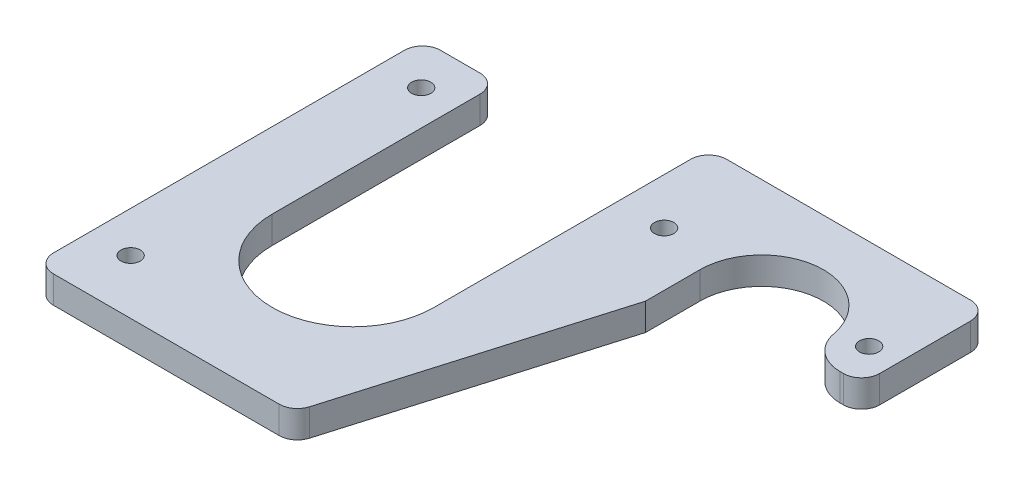
SolidWorks part; units mm, degrees
material "PC High Viscosity"
ref_plane "Front Plane" through (0, 0, 0) normal (0, 0, 1) x (1, 0, 0)
ref_plane "Top Plane" through (0, 0, 0) normal (0, 1, 0) x (1, 0, 0)
ref_plane "Right Plane" through (0, 0, 0) normal (1, 0, 0) x (0, 0, -1)
sketch "Sketch1" plane through (0, 0, 0) normal (0, 1, 0) x (1, 0, 0)
  line L0 (28.575, 81.7563) -> (28.575, 160.782)
  line L1 (0, 0) -> (180.975, 0) construction
  line L2 (0, 0) -> (0, 160.782) construction
  line L3 (28.575, 177.8) -> (180.975, 177.8) construction
  line L4 (180.975, 0) -> (180.975, 177.8) construction
  line L6 (0, 160.782) -> (0, 0)
  line L7 (0, 0) -> (82.55, 0)
  line L9 (80.9625, 81.7563) -> (80.9625, 177.8)
  line L10 (80.9625, 177.8) -> (121.7041, 177.8)
  line L13 (180.975, 139.7) -> (180.975, 177.8)
  line L14 (180.975, 177.8) -> (121.7041, 177.8)
  line L16 (118.11, 139.7) -> (118.11, 120.65)
  line L17 (82.55, 0) -> (118.11, 120.65)
  line L18 (161.29, 139.7) -> (161.29, 120.65)
  line L19 (180.975, 139.7) -> (180.975, 120.65)
  line L20 (180.975, 120.65) -> (161.29, 120.65)
  line L21 (0, 160.782) -> (28.575, 160.782)
  arc A0 (161.29, 139.7) -> (118.11, 139.7) centre (139.7, 139.7) ccw
  arc A1 (28.575, 81.7563) -> (80.9625, 81.7563) centre (54.7687, 81.7563) ccw
  dimension "D3" = 43.18
  dimension "D5" = 52.3875
  dimension "D1" = 177.8
  dimension "D2" = 180.975
  dimension "D4" = 38.1
  dimension "D6" = 81.7563
  dimension "D7" = 54.7687
  dimension "D8" = 139.7
  dimension "D9" = 19.05
  dimension "D10" = 82.55
  dimension "D11" = 121.7041
  dimension "D12" = 160.782
extrude "Boss-Extrude1" add sketch "Sketch1" along normal blind 9.525
sketch "Sketch2" plane through (0, 9.525, 0) normal (0, 1, 0) x (1, 0, 0)
  line L1 (0, 0) -> (94.3317, 0)
  line L2 (0, 0) -> (0, 25.4)
  line L3 (0, 25.4) -> (94.3317, 25.4)
  line L4 (94.3317, 0) -> (94.3317, 25.4)
  dimension "D1" = 25.4
extrude "Cut-Extrude1" cut sketch "Sketch2" against normal through all
fillet "Fillet1" radius 6.35 1 edges at (0, 4.7625, -25.4)
fillet "Fillet2" radius 6.35 4 edges at (0, 4.7625, -160.782) (180.975, 4.7625, -177.8) (180.975, 4.7625, -120.65) (90.0363, 4.7625, -25.4)
hole_wizard "1/4 Clearance Hole1" positions "Sketch3" profile "Sketch4" hole size "1/4" standard "ANSI Inch" end condition through all
sketch "Sketch3" plane through (0, 9.525, 0) normal (0, 1, 0) x (1, 0, 0)
  line L1 (28.575, 160.782) -> (6.35, 160.782) construction
  line L4 (161.29, 120.65) -> (174.625, 120.65) construction
  line L10 (99.2378, 131.2063) -> (99.2378, 177.8) construction
  line L11 (174.625, 177.8) -> (80.9625, 177.8) construction
  line L13 (17.4625, 95.25) -> (5.6328, 95.25) construction
  line L15 (0, 154.432) -> (0, 31.75) construction
  line L20 (170.9229, 130.175) -> (170.9229, 177.8) construction
  line L21 (174.625, 177.8) -> (80.9625, 177.8) construction
  line L24 (28.575, 118.8041) -> (0, 118.8041) construction
  line L25 (28.575, 81.7563) -> (28.575, 160.782) construction
  line L27 (14.2875, 118.8041) -> (14.2875, 63.4643) construction
  line L29 (118.11, 120.65) -> (118.11, 139.7) construction
  line L30 (180.975, 127) -> (180.975, 171.45) construction
  point P0 (14.2875, 146.05)
  point P2 (14.2875, 44.45)
  point P4 (99.2378, 146.05)
  point P6 (170.9229, 146.05)
  dimension "D1" = 25.4
  dimension "D2" = 14.732
  dimension "D3" = 18.8722
  dimension "D4" = 10.052
  dimension "D5" = 101.6
sketch "Sketch4" plane through (14.2875, 9.525, -146.05) normal (1, 0, 0) x (0, 0, 1)
  line L0 (0, 0) -> (0, 9.525)
  line L1 (0, 9.525) -> (3.3782, 9.525)
  line L2 (3.3782, 9.525) -> (3.3782, 0)
  line L5 (3.3782, 0) -> (0, 0)
  line L11 (0, -6.35) -> (0, 107.95) construction
  dimension "Thru Hole Dia." = 6.7564
  dimension "Thru Hole Depth" = 9.525
sketch "Sketch5" plane through (0, 9.525, 0) normal (0, 1, 0) x (1, 0, 0)
  line L0 (161.29, 133.35) -> (180.975, 133.35)
  line L1 (161.29, 139.7) -> (161.29, 120.65) construction
  line L2 (180.975, 127) -> (180.975, 171.45) construction
  line L3 (161.29, 133.35) -> (161.29, 120.65)
  line L4 (161.29, 120.65) -> (180.975, 120.65)
  line L5 (180.975, 120.65) -> (180.975, 133.35)
  line L6 (161.29, 120.65) -> (174.625, 120.65) construction
  circle A0 centre (170.9229, 146.05) radius 3.3782 construction
  dimension "D1" = 12.7
extrude "Cut-Extrude2" cut sketch "Sketch5" against normal through all
fillet "Fillet3" radius 6.35 1 edges at (180.975, 4.7625, -133.35)
sketch "Sketch6" plane through (0, 9.525, 0) normal (0, 1, 0) x (1, 0, 0)
  line L0 (26.4861, 81.7563) -> (26.4861, 177.8)
  line L1 (26.4861, 177.8) -> (83.0514, 177.8)
  line L2 (83.0514, 177.8) -> (83.0514, 81.7563)
  line L3 (174.625, 177.8) -> (80.9625, 177.8) construction
  arc A0 (26.4861, 81.7563) -> (83.0514, 81.7563) centre (54.7687, 81.7563) ccw
extrude "Cut-Extrude3" cut sketch "Sketch6" against normal through all
fillet "Fillet4" radius 12.7 1 edges at (161.29, 4.7625, -133.35)
chamfer "Chamfer1" [suppressed] distance 12.7 angle 45
fillet "Fillet5" radius 6.35 2 edges at (26.4861, 4.7625, -160.782) (83.0514, 4.7625, -177.8)
